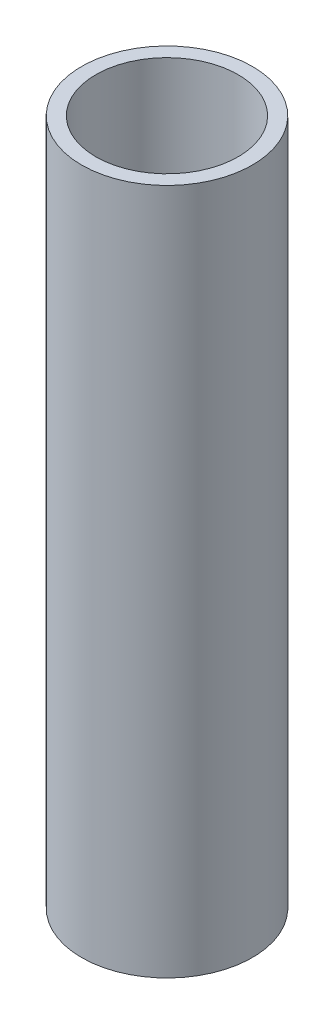
SolidWorks part; units mm, degrees
material "PLA"
ref_plane "Front Plane" through (0, 0, 0) normal (0, 0, 1) x (1, 0, 0)
ref_plane "Top Plane" through (0, 0, 0) normal (0, 1, 0) x (1, 0, 0)
ref_plane "Right Plane" through (0, 0, 0) normal (1, 0, 0) x (0, 0, -1)
sketch "Sketch1" plane through (0, 0, 0) normal (0, 1, 0) x (1, 0, 0)
  circle A0 centre (0, 0) radius 1.625
  circle A1 centre (0, 0) radius 1.95
  dimension "D1" = 3.25
  dimension "D2" = 3.9
extrude "Boss-Extrude1" add sketch "Sketch1" along normal mid plane 15.668
